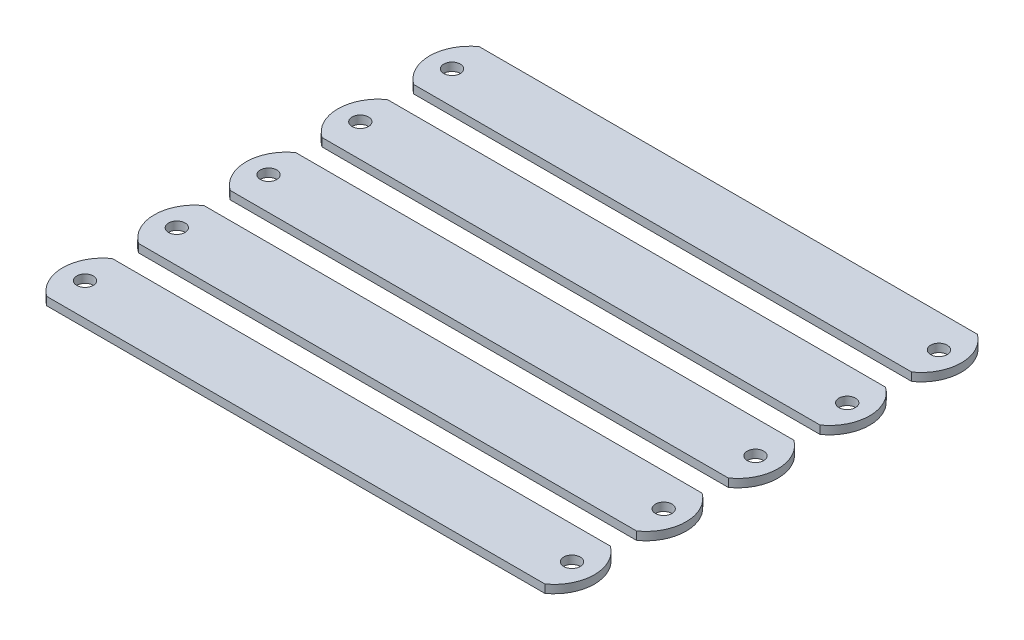
SolidWorks part; units mm, degrees
ref_plane "Front Plane" through (0, 0, 0) normal (0, 0, 1) x (1, 0, 0)
ref_plane "Top Plane" through (0, 0, 0) normal (0, 1, 0) x (1, 0, 0)
ref_plane "Right Plane" through (0, 0, 0) normal (1, 0, 0) x (0, 0, -1)
sketch "Sketch1" plane through (0, 0, 0) normal (0, 1, 0) x (1, 0, 0)
  line L0 (0, 6.35) -> (0, -6.35) construction
  line L1 (-48.26, -6.35) -> (48.26, -6.35)
  line L2 (-48.26, -6.35) -> (-48.26, 6.35)
  line L3 (-48.26, 6.35) -> (48.26, 6.35)
  line L4 (48.26, -6.35) -> (48.26, 6.35)
  line L5 (-48.26, -6.35) -> (48.26, 6.35) construction
  line L6 (-48.26, 6.35) -> (48.26, -6.35) construction
  arc A0 (-48.26, -6.35) -> (-48.26, 6.35) centre (-43.7295, 0) cw
  arc A1 (48.26, 6.35) -> (48.26, -6.35) centre (43.7295, 0) cw
  circle A2 centre (-47.1771, 0) radius 1.6002
  circle A3 centre (47.1771, 0) radius 1.6002
  point P0 (0, 0)
  point P14 (0, 0)
  point P15 (0, 0)
  point P16 (0, 0)
extrude "Boss-Extrude1" add sketch "Sketch1" along normal mid plane 1.5875 contours L1 L4 L3 L2 A2 A3 | A0 L2 | A1 L4
pattern_linear "LPattern1" count 5 spacing 17.78 along (0, 0, -1) of "Boss-Extrude1"
